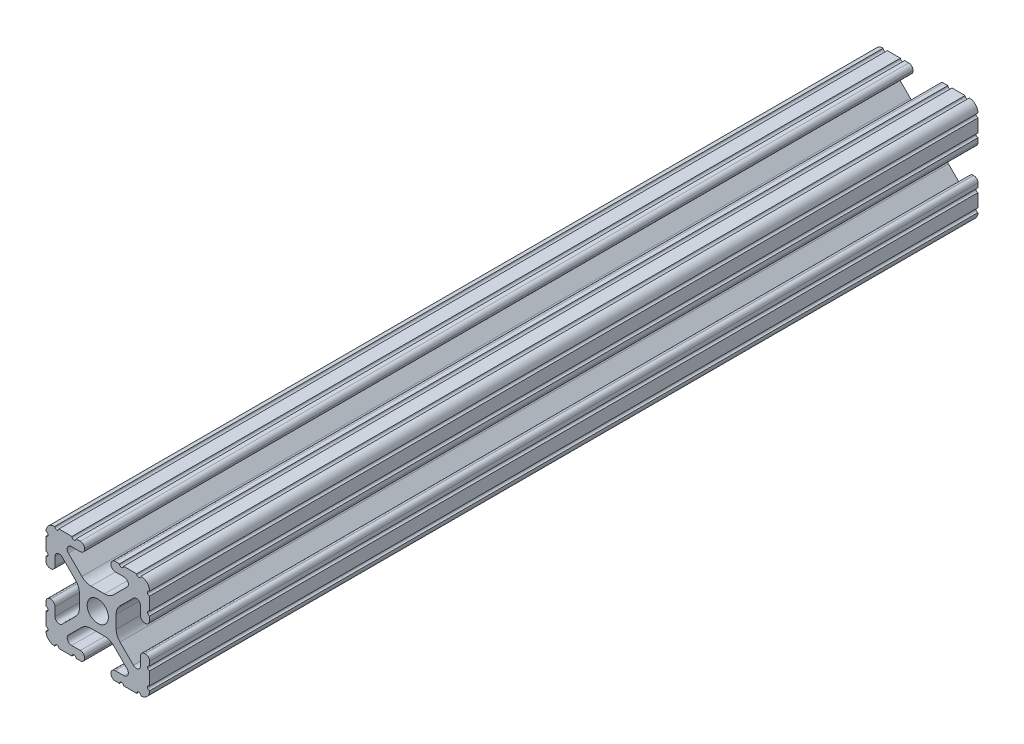
SolidWorks part; units mm, degrees
other "Markup1"
sketch "Sketch4" plane through (12.7, 12.7, 76.2) normal (0.3024, 0.6604, 0.6874) x (0.4492, 0.5373, -0.7138)
ref_plane "Front" through (0, 0, 0) normal (0, 0, 1) x (1, 0, 0)
ref_plane "Top" through (0, 0, 0) normal (0, 1, 0) x (1, 0, 0)
ref_plane "Right" through (0, 0, 0) normal (1, 0, 0) x (0, 0, -1)
sketch "Sketch1" plane through (0, 0, 0) normal (0, 0, 1) x (1, 0, 0)
  line L0 (-3.2512, 12.7) -> (-3.2512, -12.7) construction
  line L1 (-12.7, -12.7) -> (12.7, -12.7) construction
  line L2 (-12.7, -12.7) -> (-12.7, 12.7) construction
  line L3 (-12.7, 12.7) -> (12.7, 12.7) construction
  line L4 (12.7, -12.7) -> (12.7, 12.7) construction
  line L5 (0, 12.7) -> (0, -12.7) construction
  line L6 (-12.7, 0) -> (12.7, 0) construction
  line L7 (3.2512, 12.7) -> (3.2512, -12.7) construction
  line L8 (-3.2512, 12.7) -> (3.2512, -12.7) construction
  circle A0 centre (0, 0) radius 2.6035
  point P0 (0, 0)
  line B0 (-7.5107, 9.4563) -> (7.5107, 9.4563) construction
  line B1 (-7.4968, -9.4098) -> (7.4968, -9.4098) construction
  line B2 (-7.1797, -8.6452) -> (-3.9523, -5.4237)
  line B3 (-1.7093, -4.4958) -> (1.7093, -4.4958)
  line B4 (3.9523, -5.4237) -> (7.1797, -8.6452)
  line B5 (6.4164, -10.4902) -> (4.2875, -10.4902)
  line B6 (3.2385, -11.5392) -> (3.2385, -11.651)
  line B7 (4.2875, -12.7) -> (5.3171, -12.7)
  line B8 (6.3331, -12.7) -> (9.5504, -12.7)
  line B9 (12.7, -9.5504) -> (12.7, -6.3331)
  line B10 (12.7, -5.3171) -> (12.7, -4.2875)
  line B11 (11.651, -3.2385) -> (11.5392, -3.2385)
  line B12 (10.4902, -4.2875) -> (10.4902, -6.4021)
  line B13 (8.7371, -7.1294) -> (5.441, -3.8408)
  line B14 (4.5085, -1.5932) -> (4.5085, 1.5932)
  line B15 (5.441, 3.8408) -> (8.7371, 7.1294)
  line B16 (10.4902, 6.4021) -> (10.4902, 4.2875)
  line B17 (11.5392, 3.2385) -> (11.651, 3.2385)
  line B18 (12.7, 4.2875) -> (12.7, 5.3171)
  line B19 (12.7, 6.3331) -> (12.7, 9.5504)
  line B20 (9.5504, 12.7) -> (6.3331, 12.7)
  line B21 (5.3171, 12.7) -> (4.2875, 12.7)
  line B22 (3.2385, 11.651) -> (3.2385, 11.5392)
  line B23 (4.2875, 10.4902) -> (6.4768, 10.4902)
  line B24 (7.207, 8.7244) -> (3.8983, 5.4232)
  line B25 (1.6558, 4.4958) -> (-1.6558, 4.4958)
  line B26 (-3.8983, 5.4232) -> (-7.207, 8.7244)
  line B27 (-6.4768, 10.4902) -> (-4.2875, 10.4902)
  line B28 (-3.2385, 11.5392) -> (-3.2385, 11.651)
  line B29 (-4.2875, 12.7) -> (-5.3171, 12.7)
  line B30 (-6.3331, 12.7) -> (-9.5504, 12.7)
  line B31 (-12.7, 9.5504) -> (-12.7, 6.3331)
  line B32 (-12.7, 5.3171) -> (-12.7, 4.2875)
  line B33 (-11.651, 3.2385) -> (-11.5392, 3.2385)
  line B34 (-10.4902, 4.2875) -> (-10.4902, 6.4021)
  line B35 (-8.7371, 7.1294) -> (-5.441, 3.8408)
  line B36 (-4.5085, 1.5932) -> (-4.5085, -1.5932)
  line B37 (-5.441, -3.8408) -> (-8.7371, -7.1294)
  line B38 (-10.4902, -6.4021) -> (-10.4902, -4.2875)
  line B39 (-11.5392, -3.2385) -> (-11.651, -3.2385)
  line B40 (-12.7, -4.2875) -> (-12.7, -5.3171)
  line B41 (-12.7, -6.3331) -> (-12.7, -9.5504)
  line B42 (-9.5504, -12.7) -> (-6.3331, -12.7)
  line B43 (-5.3171, -12.7) -> (-4.2875, -12.7)
  line B44 (-3.2385, -11.651) -> (-3.2385, -11.5392)
  line B45 (-4.2875, -10.4902) -> (-6.4164, -10.4902)
  circle B46 centre (0, 0) radius 2.6035
  arc B47 (-7.1797, -8.6452) -> (-6.4164, -10.4902) centre (-6.4164, -9.4098) ccw
  arc B48 (-1.7093, -4.4958) -> (-3.9523, -5.4237) centre (-1.7093, -7.6708) ccw
  arc B49 (3.9523, -5.4237) -> (1.7093, -4.4958) centre (1.7093, -7.6708) ccw
  arc B50 (6.4164, -10.4902) -> (7.1797, -8.6452) centre (6.4164, -9.4098) ccw
  arc B51 (4.2875, -10.4902) -> (3.2385, -11.5392) centre (4.2875, -11.5392) ccw
  arc B52 (3.2385, -11.651) -> (4.2875, -12.7) centre (4.2875, -11.651) ccw
  arc B53 (6.3331, -12.7) -> (5.3171, -12.7) centre (5.8251, -12.7) ccw
  arc B54 (10.5664, -12.6998) -> (9.5504, -12.7) centre (10.0584, -12.7) ccw
  arc B55 (10.5664, -12.6998) -> (12.6998, -10.5664) centre (10.5918, -10.5918) ccw
  arc B56 (12.7, -9.5504) -> (12.6998, -10.5664) centre (12.7, -10.0584) ccw
  arc B57 (12.7, -5.3171) -> (12.7, -6.3331) centre (12.7, -5.8251) ccw
  arc B58 (12.7, -4.2875) -> (11.651, -3.2385) centre (11.651, -4.2875) ccw
  arc B59 (11.5392, -3.2385) -> (10.4902, -4.2875) centre (11.5392, -4.2875) ccw
  arc B60 (8.7371, -7.1294) -> (10.4902, -6.4021) centre (9.4628, -6.4021) ccw
  arc B61 (4.5085, -1.5932) -> (5.441, -3.8408) centre (7.6835, -1.5932) ccw
  arc B62 (5.441, 3.8408) -> (4.5085, 1.5932) centre (7.6835, 1.5932) ccw
  arc B63 (10.4902, 6.4021) -> (8.7371, 7.1294) centre (9.4628, 6.4021) ccw
  arc B64 (10.4902, 4.2875) -> (11.5392, 3.2385) centre (11.5392, 4.2875) ccw
  arc B65 (11.651, 3.2385) -> (12.7, 4.2875) centre (11.651, 4.2875) ccw
  arc B66 (12.7, 6.3331) -> (12.7, 5.3171) centre (12.7, 5.8251) ccw
  arc B67 (12.6998, 10.5664) -> (12.7, 9.5504) centre (12.7, 10.0584) ccw
  arc B68 (12.6998, 10.5664) -> (10.5664, 12.6998) centre (10.5918, 10.5918) ccw
  arc B69 (9.5504, 12.7) -> (10.5664, 12.6998) centre (10.0584, 12.7) ccw
  arc B70 (5.3171, 12.7) -> (6.3331, 12.7) centre (5.8251, 12.7) ccw
  arc B71 (4.2875, 12.7) -> (3.2385, 11.651) centre (4.2875, 11.651) ccw
  arc B72 (3.2385, 11.5392) -> (4.2875, 10.4902) centre (4.2875, 11.5392) ccw
  arc B73 (7.207, 8.7244) -> (6.4768, 10.4902) centre (6.4768, 9.4563) ccw
  arc B74 (1.6558, 4.4958) -> (3.8983, 5.4232) centre (1.6558, 7.6708) ccw
  arc B75 (-3.8983, 5.4232) -> (-1.6558, 4.4958) centre (-1.6558, 7.6708) ccw
  arc B76 (-6.4768, 10.4902) -> (-7.207, 8.7244) centre (-6.4768, 9.4563) ccw
  arc B77 (-4.2875, 10.4902) -> (-3.2385, 11.5392) centre (-4.2875, 11.5392) ccw
  arc B78 (-3.2385, 11.651) -> (-4.2875, 12.7) centre (-4.2875, 11.651) ccw
  arc B79 (-6.3331, 12.7) -> (-5.3171, 12.7) centre (-5.8251, 12.7) ccw
  arc B80 (-10.5664, 12.6998) -> (-9.5504, 12.7) centre (-10.0584, 12.7) ccw
  arc B81 (-10.5664, 12.6998) -> (-12.6998, 10.5664) centre (-10.5918, 10.5918) ccw
  arc B82 (-12.7, 9.5504) -> (-12.6998, 10.5664) centre (-12.7, 10.0584) ccw
  arc B83 (-12.7, 5.3171) -> (-12.7, 6.3331) centre (-12.7, 5.8251) ccw
  arc B84 (-12.7, 4.2875) -> (-11.651, 3.2385) centre (-11.651, 4.2875) ccw
  arc B85 (-11.5392, 3.2385) -> (-10.4902, 4.2875) centre (-11.5392, 4.2875) ccw
  arc B86 (-8.7371, 7.1294) -> (-10.4902, 6.4021) centre (-9.4628, 6.4021) ccw
  arc B87 (-4.5085, 1.5932) -> (-5.441, 3.8408) centre (-7.6835, 1.5932) ccw
  arc B88 (-5.441, -3.8408) -> (-4.5085, -1.5932) centre (-7.6835, -1.5932) ccw
  arc B89 (-10.4902, -6.4021) -> (-8.7371, -7.1294) centre (-9.4628, -6.4021) ccw
  arc B90 (-10.4902, -4.2875) -> (-11.5392, -3.2385) centre (-11.5392, -4.2875) ccw
  arc B91 (-11.651, -3.2385) -> (-12.7, -4.2875) centre (-11.651, -4.2875) ccw
  arc B92 (-12.7, -6.3331) -> (-12.7, -5.3171) centre (-12.7, -5.8251) ccw
  arc B93 (-12.6998, -10.5664) -> (-12.7, -9.5504) centre (-12.7, -10.0584) ccw
  arc B94 (-12.6998, -10.5664) -> (-10.5664, -12.6998) centre (-10.5918, -10.5918) ccw
  arc B95 (-9.5504, -12.7) -> (-10.5664, -12.6998) centre (-10.0584, -12.7) ccw
  arc B96 (-5.3171, -12.7) -> (-6.3331, -12.7) centre (-5.8251, -12.7) ccw
  arc B97 (-4.2875, -12.7) -> (-3.2385, -11.651) centre (-4.2875, -11.651) ccw
  arc B98 (-3.2385, -11.5392) -> (-4.2875, -10.4902) centre (-4.2875, -11.5392) ccw
  dimension "Center Hole Diameter" = 5.207
  dimension "Rail Width" = 25.4
  dimension "Rail Height" = 25.4
  dimension "T-Slot Width" = 6.5024
sketch_block_instance "Block1-1"
sketch_block "Block1"
sketch "Sketch2" plane through (0, 0, 0) normal (1, 0, 0) x (0, 0, -1)
  line L0 (-76.2, 0) -> (76.2, 0) construction
  line L1 (0, 0) -> (0, 12.7) construction
  line L2 (12.7, 12.7) -> (-12.7, 12.7) construction
  line L3 (-3048, -12.7) -> (3048, -12.7) construction
  line L4 (-45.72, 0) -> (0, 12.7) construction
  line L5 (0, 12.7) -> (45.72, 0) construction
  point P5 (-45.72, 0)
  point P9 (0, 12.7)
  point P12 (45.72, 0)
  dimension "Length Range [Min]" = 25.4
  dimension "Rep Length" = 152.4
  dimension "Length Range [Max]" = 6096
  dimension "D1" = 91.44
sketch "Sketch3" plane through (0, 0, 0) normal (0, 0, 1) x (1, 0, 0)
  line L0 (-7.1797, -8.6452) -> (-3.9523, -5.4237) construction
  line L1 (-4.2875, -10.4902) -> (-6.4164, -10.4902) construction
  line L2 (-3.2385, -11.651) -> (-3.2385, -11.5392) construction
  line L3 (-5.3171, -12.7) -> (-4.2875, -12.7) construction
  line L4 (-9.5504, -12.7) -> (-6.3331, -12.7) construction
  line L5 (-12.7, -6.3331) -> (-12.7, -9.5504) construction
  line L6 (-12.7, -4.2875) -> (-12.7, -5.3171) construction
  line L7 (-11.5392, -3.2385) -> (-11.651, -3.2385) construction
  line L8 (-10.4902, -6.4021) -> (-10.4902, -4.2875) construction
  line L9 (-5.441, -3.8408) -> (-8.7371, -7.1294) construction
  line L10 (-4.5085, 1.5932) -> (-4.5085, -1.5932) construction
  line L11 (-8.7371, 7.1294) -> (-5.441, 3.8408) construction
  line L12 (-10.4902, 4.2875) -> (-10.4902, 6.4021) construction
  line L13 (-11.651, 3.2385) -> (-11.5392, 3.2385) construction
  line L14 (-12.7, 5.3171) -> (-12.7, 4.2875) construction
  line L15 (-12.7, 9.5504) -> (-12.7, 6.3331) construction
  line L16 (-6.3331, 12.7) -> (-9.5504, 12.7) construction
  line L17 (-4.2875, 12.7) -> (-5.3171, 12.7) construction
  line L18 (-3.2385, 11.5392) -> (-3.2385, 11.651) construction
  line L19 (-6.4768, 10.4902) -> (-4.2875, 10.4902) construction
  line L20 (-3.8983, 5.4232) -> (-7.207, 8.7244) construction
  line L21 (1.6558, 4.4958) -> (-1.6558, 4.4958) construction
  line L22 (7.207, 8.7244) -> (3.8983, 5.4232) construction
  line L23 (4.2875, 10.4902) -> (6.4768, 10.4902) construction
  line L24 (3.2385, 11.651) -> (3.2385, 11.5392) construction
  line L25 (5.3171, 12.7) -> (4.2875, 12.7) construction
  line L26 (9.5504, 12.7) -> (6.3331, 12.7) construction
  line L27 (12.7, 6.3331) -> (12.7, 9.5504) construction
  line L28 (12.7, 4.2875) -> (12.7, 5.3171) construction
  line L29 (11.5392, 3.2385) -> (11.651, 3.2385) construction
  line L30 (10.4902, 6.4021) -> (10.4902, 4.2875) construction
  line L31 (5.441, 3.8408) -> (8.7371, 7.1294) construction
  line L32 (4.5085, -1.5932) -> (4.5085, 1.5932) construction
  line L33 (8.7371, -7.1294) -> (5.441, -3.8408) construction
  line L34 (10.4902, -4.2875) -> (10.4902, -6.4021) construction
  line L35 (11.651, -3.2385) -> (11.5392, -3.2385) construction
  line L36 (12.7, -5.3171) -> (12.7, -4.2875) construction
  line L37 (12.7, -9.5504) -> (12.7, -6.3331) construction
  line L38 (6.3331, -12.7) -> (9.5504, -12.7) construction
  line L39 (4.2875, -12.7) -> (5.3171, -12.7) construction
  line L40 (3.2385, -11.5392) -> (3.2385, -11.651) construction
  line L41 (6.4164, -10.4902) -> (4.2875, -10.4902) construction
  line L42 (3.9523, -5.4237) -> (7.1797, -8.6452) construction
  line L43 (-1.7093, -4.4958) -> (1.7093, -4.4958) construction
  line L44 (-7.1797, -8.6452) -> (-3.9523, -5.4237)
  line L45 (-4.2875, -10.4902) -> (-6.4164, -10.4902)
  line L46 (-3.2385, -11.651) -> (-3.2385, -11.5392)
  line L47 (-5.3171, -12.7) -> (-4.2875, -12.7)
  line L48 (-9.5504, -12.7) -> (-6.3331, -12.7)
  line L49 (-12.7, -6.3331) -> (-12.7, -9.5504)
  line L50 (-12.7, -4.2875) -> (-12.7, -5.3171)
  line L51 (-11.5392, -3.2385) -> (-11.651, -3.2385)
  line L52 (-10.4902, -6.4021) -> (-10.4902, -4.2875)
  line L53 (-5.441, -3.8408) -> (-8.7371, -7.1294)
  line L54 (-4.5085, 1.5932) -> (-4.5085, -1.5932)
  line L55 (-8.7371, 7.1294) -> (-5.441, 3.8408)
  line L56 (-10.4902, 4.2875) -> (-10.4902, 6.4021)
  line L57 (-11.651, 3.2385) -> (-11.5392, 3.2385)
  line L58 (-12.7, 5.3171) -> (-12.7, 4.2875)
  line L59 (-12.7, 9.5504) -> (-12.7, 6.3331)
  line L60 (-6.3331, 12.7) -> (-9.5504, 12.7)
  line L61 (-4.2875, 12.7) -> (-5.3171, 12.7)
  line L62 (-3.2385, 11.5392) -> (-3.2385, 11.651)
  line L63 (-6.4768, 10.4902) -> (-4.2875, 10.4902)
  line L64 (-3.8983, 5.4232) -> (-7.207, 8.7244)
  line L65 (1.6558, 4.4958) -> (-1.6558, 4.4958)
  line L66 (7.207, 8.7244) -> (3.8983, 5.4232)
  line L67 (4.2875, 10.4902) -> (6.4768, 10.4902)
  line L68 (3.2385, 11.651) -> (3.2385, 11.5392)
  line L69 (5.3171, 12.7) -> (4.2875, 12.7)
  line L70 (9.5504, 12.7) -> (6.3331, 12.7)
  line L71 (12.7, 6.3331) -> (12.7, 9.5504)
  line L72 (12.7, 4.2875) -> (12.7, 5.3171)
  line L73 (11.5392, 3.2385) -> (11.651, 3.2385)
  line L74 (10.4902, 6.4021) -> (10.4902, 4.2875)
  line L75 (5.441, 3.8408) -> (8.7371, 7.1294)
  line L76 (4.5085, -1.5932) -> (4.5085, 1.5932)
  line L77 (8.7371, -7.1294) -> (5.441, -3.8408)
  line L78 (10.4902, -4.2875) -> (10.4902, -6.4021)
  line L79 (11.651, -3.2385) -> (11.5392, -3.2385)
  line L80 (12.7, -5.3171) -> (12.7, -4.2875)
  line L81 (12.7, -9.5504) -> (12.7, -6.3331)
  line L82 (6.3331, -12.7) -> (9.5504, -12.7)
  line L83 (4.2875, -12.7) -> (5.3171, -12.7)
  line L84 (3.2385, -11.5392) -> (3.2385, -11.651)
  line L85 (6.4164, -10.4902) -> (4.2875, -10.4902)
  line L86 (3.9523, -5.4237) -> (7.1797, -8.6452)
  line L87 (-1.7093, -4.4958) -> (1.7093, -4.4958)
  circle A0 centre (0, 0) radius 2.6035 construction
  circle A1 centre (0, 0) radius 2.6035
  circle A2 centre (0, 0) radius 2.6035
  arc A3 (-1.7093, -4.4958) -> (-3.9523, -5.4237) centre (-1.7093, -7.6708) ccw construction
  arc A4 (-7.1797, -8.6452) -> (-6.4164, -10.4902) centre (-6.4164, -9.4098) ccw construction
  arc A5 (-3.2385, -11.5392) -> (-4.2875, -10.4902) centre (-4.2875, -11.5392) ccw construction
  arc A6 (-4.2875, -12.7) -> (-3.2385, -11.651) centre (-4.2875, -11.651) ccw construction
  arc A7 (-5.3171, -12.7) -> (-6.3331, -12.7) centre (-5.8251, -12.7) ccw construction
  arc A8 (-9.5504, -12.7) -> (-10.5664, -12.6998) centre (-10.0584, -12.7) ccw construction
  arc A9 (-12.6998, -10.5664) -> (-10.5664, -12.6998) centre (-10.5918, -10.5918) ccw construction
  arc A10 (-12.6998, -10.5664) -> (-12.7, -9.5504) centre (-12.7, -10.0584) ccw construction
  arc A11 (-12.7, -6.3331) -> (-12.7, -5.3171) centre (-12.7, -5.8251) ccw construction
  arc A12 (-11.651, -3.2385) -> (-12.7, -4.2875) centre (-11.651, -4.2875) ccw construction
  arc A13 (-10.4902, -4.2875) -> (-11.5392, -3.2385) centre (-11.5392, -4.2875) ccw construction
  arc A14 (-10.4902, -6.4021) -> (-8.7371, -7.1294) centre (-9.4628, -6.4021) ccw construction
  arc A15 (-5.441, -3.8408) -> (-4.5085, -1.5932) centre (-7.6835, -1.5932) ccw construction
  arc A16 (-4.5085, 1.5932) -> (-5.441, 3.8408) centre (-7.6835, 1.5932) ccw construction
  arc A17 (-8.7371, 7.1294) -> (-10.4902, 6.4021) centre (-9.4628, 6.4021) ccw construction
  arc A18 (-11.5392, 3.2385) -> (-10.4902, 4.2875) centre (-11.5392, 4.2875) ccw construction
  arc A19 (-12.7, 4.2875) -> (-11.651, 3.2385) centre (-11.651, 4.2875) ccw construction
  arc A20 (-12.7, 5.3171) -> (-12.7, 6.3331) centre (-12.7, 5.8251) ccw construction
  arc A21 (-12.7, 9.5504) -> (-12.6998, 10.5664) centre (-12.7, 10.0584) ccw construction
  arc A22 (-10.5664, 12.6998) -> (-12.6998, 10.5664) centre (-10.5918, 10.5918) ccw construction
  arc A23 (-10.5664, 12.6998) -> (-9.5504, 12.7) centre (-10.0584, 12.7) ccw construction
  arc A24 (-6.3331, 12.7) -> (-5.3171, 12.7) centre (-5.8251, 12.7) ccw construction
  arc A25 (-3.2385, 11.651) -> (-4.2875, 12.7) centre (-4.2875, 11.651) ccw construction
  arc A26 (-4.2875, 10.4902) -> (-3.2385, 11.5392) centre (-4.2875, 11.5392) ccw construction
  arc A27 (-6.4768, 10.4902) -> (-7.207, 8.7244) centre (-6.4768, 9.4563) ccw construction
  arc A28 (-3.8983, 5.4232) -> (-1.6558, 4.4958) centre (-1.6558, 7.6708) ccw construction
  arc A29 (1.6558, 4.4958) -> (3.8983, 5.4232) centre (1.6558, 7.6708) ccw construction
  arc A30 (7.207, 8.7244) -> (6.4768, 10.4902) centre (6.4768, 9.4563) ccw construction
  arc A31 (3.2385, 11.5392) -> (4.2875, 10.4902) centre (4.2875, 11.5392) ccw construction
  arc A32 (4.2875, 12.7) -> (3.2385, 11.651) centre (4.2875, 11.651) ccw construction
  arc A33 (5.3171, 12.7) -> (6.3331, 12.7) centre (5.8251, 12.7) ccw construction
  arc A34 (9.5504, 12.7) -> (10.5664, 12.6998) centre (10.0584, 12.7) ccw construction
  arc A35 (12.6998, 10.5664) -> (10.5664, 12.6998) centre (10.5918, 10.5918) ccw construction
  arc A36 (12.6998, 10.5664) -> (12.7, 9.5504) centre (12.7, 10.0584) ccw construction
  arc A37 (12.7, 6.3331) -> (12.7, 5.3171) centre (12.7, 5.8251) ccw construction
  arc A38 (11.651, 3.2385) -> (12.7, 4.2875) centre (11.651, 4.2875) ccw construction
  arc A39 (10.4902, 4.2875) -> (11.5392, 3.2385) centre (11.5392, 4.2875) ccw construction
  arc A40 (10.4902, 6.4021) -> (8.7371, 7.1294) centre (9.4628, 6.4021) ccw construction
  arc A41 (5.441, 3.8408) -> (4.5085, 1.5932) centre (7.6835, 1.5932) ccw construction
  arc A42 (4.5085, -1.5932) -> (5.441, -3.8408) centre (7.6835, -1.5932) ccw construction
  arc A43 (8.7371, -7.1294) -> (10.4902, -6.4021) centre (9.4628, -6.4021) ccw construction
  arc A44 (11.5392, -3.2385) -> (10.4902, -4.2875) centre (11.5392, -4.2875) ccw construction
  arc A45 (12.7, -4.2875) -> (11.651, -3.2385) centre (11.651, -4.2875) ccw construction
  arc A46 (12.7, -5.3171) -> (12.7, -6.3331) centre (12.7, -5.8251) ccw construction
  arc A47 (12.7, -9.5504) -> (12.6998, -10.5664) centre (12.7, -10.0584) ccw construction
  arc A48 (10.5664, -12.6998) -> (12.6998, -10.5664) centre (10.5918, -10.5918) ccw construction
  arc A49 (10.5664, -12.6998) -> (9.5504, -12.7) centre (10.0584, -12.7) ccw construction
  arc A50 (6.3331, -12.7) -> (5.3171, -12.7) centre (5.8251, -12.7) ccw construction
  arc A51 (3.2385, -11.651) -> (4.2875, -12.7) centre (4.2875, -11.651) ccw construction
  arc A52 (4.2875, -10.4902) -> (3.2385, -11.5392) centre (4.2875, -11.5392) ccw construction
  arc A53 (6.4164, -10.4902) -> (7.1797, -8.6452) centre (6.4164, -9.4098) ccw construction
  arc A54 (3.9523, -5.4237) -> (1.7093, -4.4958) centre (1.7093, -7.6708) ccw construction
  circle A55 centre (0, 0) radius 2.6035
  arc A56 (-1.7093, -4.4958) -> (-3.9523, -5.4237) centre (-1.7093, -7.6708) ccw
  arc A57 (-7.1797, -8.6452) -> (-6.4164, -10.4902) centre (-6.4164, -9.4098) ccw
  arc A58 (-3.2385, -11.5392) -> (-4.2875, -10.4902) centre (-4.2875, -11.5392) ccw
  arc A59 (-4.2875, -12.7) -> (-3.2385, -11.651) centre (-4.2875, -11.651) ccw
  arc A60 (-5.3171, -12.7) -> (-6.3331, -12.7) centre (-5.8251, -12.7) ccw
  arc A61 (-9.5504, -12.7) -> (-10.5664, -12.6998) centre (-10.0584, -12.7) ccw
  arc A62 (-12.6998, -10.5664) -> (-10.5664, -12.6998) centre (-10.5918, -10.5918) ccw
  arc A63 (-12.6998, -10.5664) -> (-12.7, -9.5504) centre (-12.7, -10.0584) ccw
  arc A64 (-12.7, -6.3331) -> (-12.7, -5.3171) centre (-12.7, -5.8251) ccw
  arc A65 (-11.651, -3.2385) -> (-12.7, -4.2875) centre (-11.651, -4.2875) ccw
  arc A66 (-10.4902, -4.2875) -> (-11.5392, -3.2385) centre (-11.5392, -4.2875) ccw
  arc A67 (-10.4902, -6.4021) -> (-8.7371, -7.1294) centre (-9.4628, -6.4021) ccw
  arc A68 (-5.441, -3.8408) -> (-4.5085, -1.5932) centre (-7.6835, -1.5932) ccw
  arc A69 (-4.5085, 1.5932) -> (-5.441, 3.8408) centre (-7.6835, 1.5932) ccw
  arc A70 (-8.7371, 7.1294) -> (-10.4902, 6.4021) centre (-9.4628, 6.4021) ccw
  arc A71 (-11.5392, 3.2385) -> (-10.4902, 4.2875) centre (-11.5392, 4.2875) ccw
  arc A72 (-12.7, 4.2875) -> (-11.651, 3.2385) centre (-11.651, 4.2875) ccw
  arc A73 (-12.7, 5.3171) -> (-12.7, 6.3331) centre (-12.7, 5.8251) ccw
  arc A74 (-12.7, 9.5504) -> (-12.6998, 10.5664) centre (-12.7, 10.0584) ccw
  arc A75 (-10.5664, 12.6998) -> (-12.6998, 10.5664) centre (-10.5918, 10.5918) ccw
  arc A76 (-10.5664, 12.6998) -> (-9.5504, 12.7) centre (-10.0584, 12.7) ccw
  arc A77 (-6.3331, 12.7) -> (-5.3171, 12.7) centre (-5.8251, 12.7) ccw
  arc A78 (-3.2385, 11.651) -> (-4.2875, 12.7) centre (-4.2875, 11.651) ccw
  arc A79 (-4.2875, 10.4902) -> (-3.2385, 11.5392) centre (-4.2875, 11.5392) ccw
  arc A80 (-6.4768, 10.4902) -> (-7.207, 8.7244) centre (-6.4768, 9.4563) ccw
  arc A81 (-3.8983, 5.4232) -> (-1.6558, 4.4958) centre (-1.6558, 7.6708) ccw
  arc A82 (1.6558, 4.4958) -> (3.8983, 5.4232) centre (1.6558, 7.6708) ccw
  arc A83 (7.207, 8.7244) -> (6.4768, 10.4902) centre (6.4768, 9.4563) ccw
  arc A84 (3.2385, 11.5392) -> (4.2875, 10.4902) centre (4.2875, 11.5392) ccw
  arc A85 (4.2875, 12.7) -> (3.2385, 11.651) centre (4.2875, 11.651) ccw
  arc A86 (5.3171, 12.7) -> (6.3331, 12.7) centre (5.8251, 12.7) ccw
  arc A87 (9.5504, 12.7) -> (10.5664, 12.6998) centre (10.0584, 12.7) ccw
  arc A88 (12.6998, 10.5664) -> (10.5664, 12.6998) centre (10.5918, 10.5918) ccw
  arc A89 (12.6998, 10.5664) -> (12.7, 9.5504) centre (12.7, 10.0584) ccw
  arc A90 (12.7, 6.3331) -> (12.7, 5.3171) centre (12.7, 5.8251) ccw
  arc A91 (11.651, 3.2385) -> (12.7, 4.2875) centre (11.651, 4.2875) ccw
  arc A92 (10.4902, 4.2875) -> (11.5392, 3.2385) centre (11.5392, 4.2875) ccw
  arc A93 (10.4902, 6.4021) -> (8.7371, 7.1294) centre (9.4628, 6.4021) ccw
  arc A94 (5.441, 3.8408) -> (4.5085, 1.5932) centre (7.6835, 1.5932) ccw
  arc A95 (4.5085, -1.5932) -> (5.441, -3.8408) centre (7.6835, -1.5932) ccw
  arc A96 (8.7371, -7.1294) -> (10.4902, -6.4021) centre (9.4628, -6.4021) ccw
  arc A97 (11.5392, -3.2385) -> (10.4902, -4.2875) centre (11.5392, -4.2875) ccw
  arc A98 (12.7, -4.2875) -> (11.651, -3.2385) centre (11.651, -4.2875) ccw
  arc A99 (12.7, -5.3171) -> (12.7, -6.3331) centre (12.7, -5.8251) ccw
  arc A100 (12.7, -9.5504) -> (12.6998, -10.5664) centre (12.7, -10.0584) ccw
  arc A101 (10.5664, -12.6998) -> (12.6998, -10.5664) centre (10.5918, -10.5918) ccw
  arc A102 (10.5664, -12.6998) -> (9.5504, -12.7) centre (10.0584, -12.7) ccw
  arc A103 (6.3331, -12.7) -> (5.3171, -12.7) centre (5.8251, -12.7) ccw
  arc A104 (3.2385, -11.651) -> (4.2875, -12.7) centre (4.2875, -11.651) ccw
  arc A105 (4.2875, -10.4902) -> (3.2385, -11.5392) centre (4.2875, -11.5392) ccw
  arc A106 (6.4164, -10.4902) -> (7.1797, -8.6452) centre (6.4164, -9.4098) ccw
  arc A107 (3.9523, -5.4237) -> (1.7093, -4.4958) centre (1.7093, -7.6708) ccw
  dimension "D1" = 0
extrude "Boss-Extrude1" add sketch "Sketch3" along normal mid plane 203.2 contours A56 L44 A57 L45 A58 L46 A59 L47 A60 L48 A61 A62 A63 L49 A64 L50 A65 L51 A66 L52 A67 L53 A68 L54 A69 L55 A70 L56 A71 L57 A72 L58 A73 L59 A74 A75 A76 L60 A77 L61 A78 L62 A79 L63 A80 L64 A81 L65 A82 L66 A83 L67 A84 L68 A85 L69 A86 L70 A87 A88 A89 L71 A90 L72 A91 L73 A92 L74 A93 L75 A94 L76 A95 L77 A96 L78 A97 L79 A98 L80 A99 L81 A100 A101 A102 L82 A103 L83 A104 L84 A105 L85 A106 L86 A107 L87 | A2
equation "\"D1@Sketch2\"=\"Rep Length@Sketch2\"*.6"
